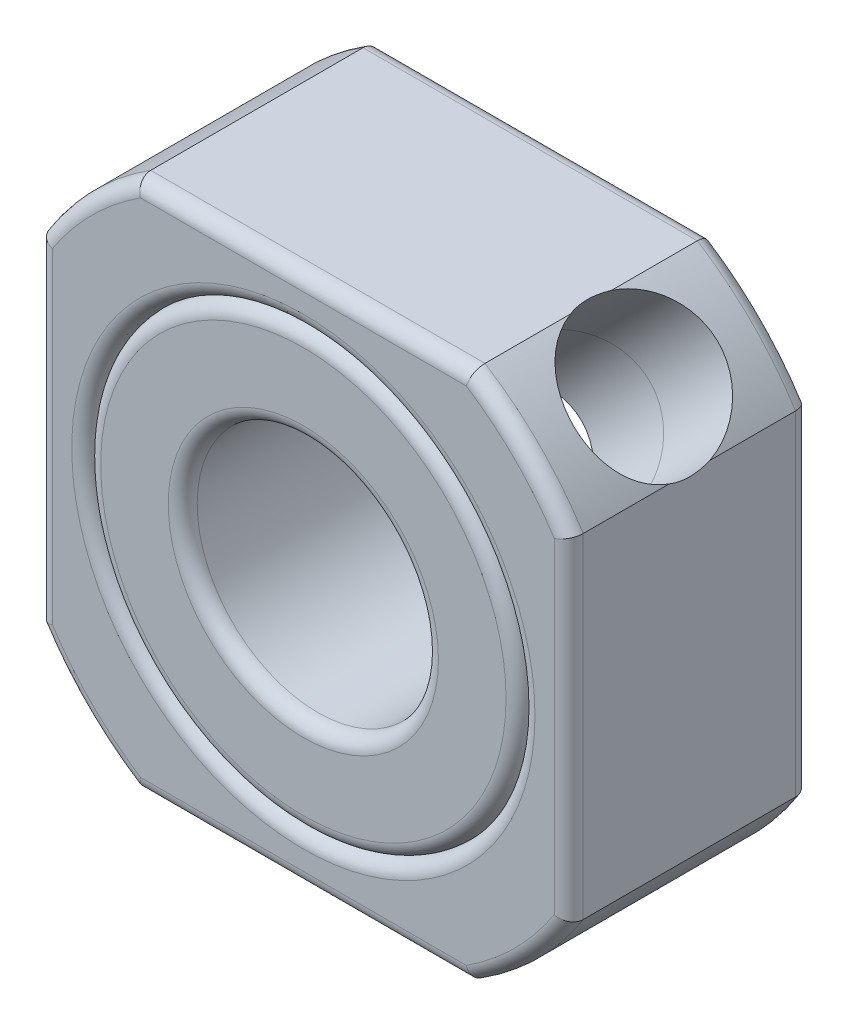
SolidWorks part; units mm, degrees
ref_plane "Front Plane" through (0, 0, 0) normal (0, 0, 1) x (1, 0, 0)
ref_plane "Top Plane" through (0, 0, 0) normal (0, 1, 0) x (1, 0, 0)
ref_plane "Right Plane" through (0, 0, 0) normal (1, 0, 0) x (0, 0, -1)
sketch "Sketch1" plane through (0, 0, 0) normal (0, 0, 1) x (1, 0, 0)
  line L0 (0, -5.5) -> (0, 5.5) construction
  line L1 (-5.5, 0) -> (5.5, 0) construction
  line L3 (-5.5, 5.5) -> (5.5, 5.5)
  line L4 (-5.5, 5.5) -> (-5.5, -5.5)
  line L5 (-5.5, -5.5) -> (5.5, -5.5)
  line L6 (5.5, 5.5) -> (5.5, -5.5)
  point P4 (0, 0)
  point P8 (0, 0)
  dimension "T" = 11
  dimension "D1" = 11
extrude "Boss-Extrude1" add sketch "Sketch1" against normal blind 5
sketch "Sketch2" plane through (0, 0, 0) normal (0, 0, 1) x (1, 0, 0)
  circle A0 centre (0, 0) radius 6.5
  dimension "D" = 13
extrude "Cut-Extrude2" cut sketch "Sketch2" against normal blind 5 flip side to cut
sketch "Sketch3" plane through (0, 0, 0) normal (0, 0, 1) x (1, 0, 0)
  circle A0 centre (0, 0) radius 4.5
  dimension "d" = 9
extrude "Cut-Extrude3" cut sketch "Sketch3" against normal blind 5
sketch "Sketch4" plane through (0, 0, 0) normal (0, 0, 1) x (1, 0, 0)
  circle A0 centre (0, 0) radius 4.5
  circle A1 centre (0, 0) radius 2.5
  dimension "D1" = 9
  dimension "M" = 5
extrude "Boss-Extrude2" add sketch "Sketch4" against normal blind 5 separate body
fillet "Fillet1" radius 0.3 18 edges at (4.5, 0, 0) (4.5962, -4.5962, 0) (0, -5.5, 0) (-4.5962, -4.5962, 0) (-5.5, 0, 0) (-4.5962, 4.5962, 0) (0, 5.5, 0) (4.5962, 4.5962, 0) (5.5, 0, 0) (0, 5.5, -5) (-4.5962, 4.5962, -5) (-5.5, 0, -5) (-4.5962, -4.5962, -5) (0, -5.5, -5) (4.5962, -4.5962, -5) (5.5, 0, -5) (4.5962, 4.5962, -5) (4.5, 0, -5)
fillet "Fillet2" radius 0.3 4 edges at (4.5, 0, -5) (2.5, 0, -5) (4.5, 0, 0) (2.5, 0, 0)
ref_plane "Plane1" through (4.5962, 4.5962, 0) normal (0.7071, 0.7071, 0) x (0, 0, 1)
sketch "Sketch5" plane through (4.5962, 4.5962, 0) normal (0.7071, 0.7071, 0) x (0, 0, 1)
  line L0 (-4.7, 0) -> (-0.3, 0) construction
  line L1 (-4.7, 1.4396) -> (-4.7, -1.4396) construction
  line L2 (-0.3, -1.4396) -> (-0.3, 1.4396) construction
  line L3 (-2.5, 1.4396) -> (-2.5, -1.4396) construction
  line L4 (-4.7, 1.4396) -> (-0.3, 1.4396) construction
  line L5 (-0.3, -1.4396) -> (-4.7, -1.4396) construction
  circle A0 centre (-2.5, 0) radius 1.5
  dimension "m" = 3
extrude "Cut-Extrude4" cut sketch "Sketch5" against normal blind 8
equation "\"D1@Sketch1\"=\"T@Sketch1\""
equation "\"D1@Cut-Extrude2\"=\"h@Boss-Extrude1\""
equation "\"D1@Cut-Extrude3\"=\"h@Boss-Extrude1\""
equation "\"D1@Sketch4\"=\"d@Sketch3\""
equation "\"D1@Boss-Extrude2\"=\"h@Boss-Extrude1\""
equation "\"D1@Cut-Extrude4\"=\"D@Sketch2\"-\"M@Sketch4\""
